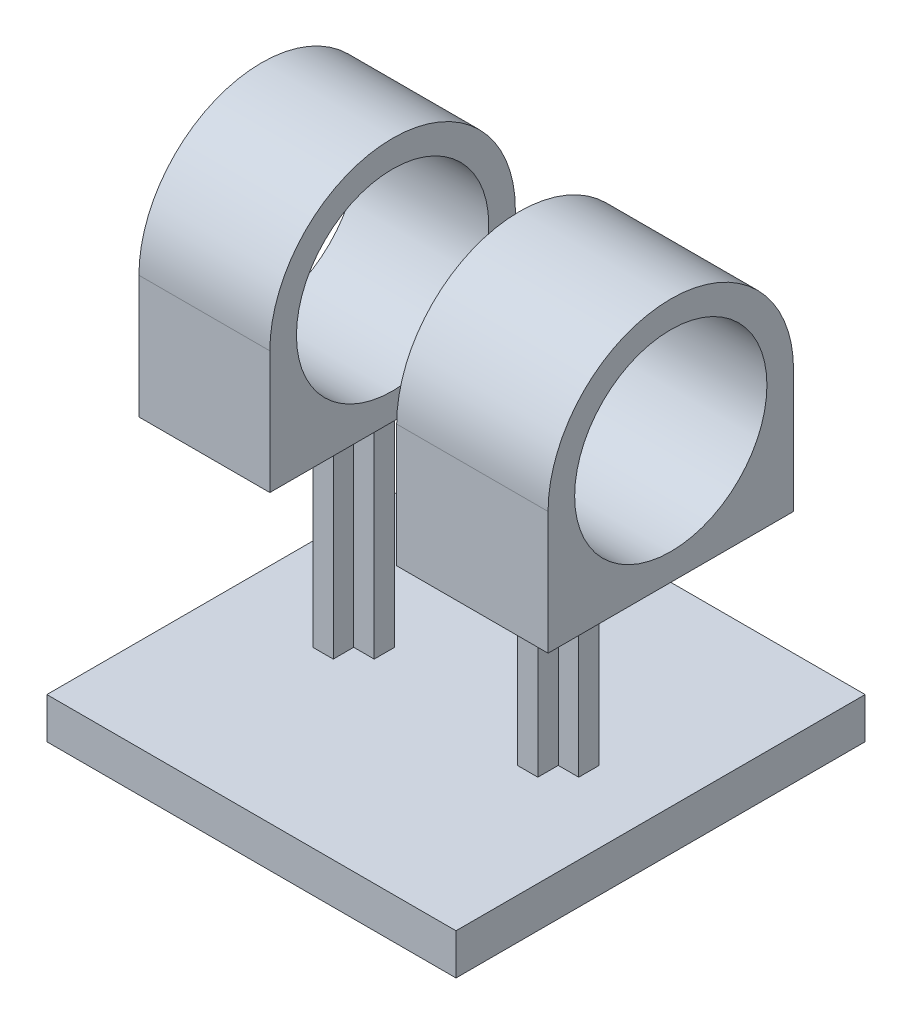
SolidWorks part; units mm, degrees
ref_plane "Plan de face" through (0, 0, 0) normal (0, 0, 1) x (1, 0, 0)
ref_plane "Plan de dessus" through (0, 0, 0) normal (0, 1, 0) x (1, 0, 0)
ref_plane "Plan de droite" through (0, 0, 0) normal (1, 0, 0) x (0, 0, -1)
sketch "Esquisse1" plane through (0, 0, 0) normal (0, 1, 0) x (1, 0, 0)
  line L1 (50, -50) -> (-50, -50)
  line L2 (50, -50) -> (50, 50)
  line L3 (50, 50) -> (-50, 50)
  line L4 (-50, -50) -> (-50, 50)
  line L5 (50, -50) -> (-50, 50) construction
  line L6 (50, 50) -> (-50, -50) construction
  point P0 (0, 0)
  dimension "D1" = 100
extrude "Boss.-Extru.1" add sketch "Esquisse1" along normal blind 10
sketch "Esquisse2" plane through (0, 10, 0) normal (0, 1, 0) x (1, 0, 0)
  line L0 (-25, 0) -> (25, 0) construction
  line L1 (-27.5, 2.5) -> (-27.5, 7.5)
  line L2 (-22.5, -7.5) -> (-27.5, -7.5)
  line L3 (-22.5, -7.5) -> (-22.5, -2.5)
  line L4 (-22.5, 7.5) -> (-27.5, 7.5)
  line L5 (-27.5, -7.5) -> (-27.5, -2.5)
  line L6 (-27.5, 2.5) -> (-22.5, -2.5) construction
  line L7 (-22.5, 2.5) -> (-22.5, 7.5)
  line L8 (-17.5, -2.5) -> (-22.5, -2.5)
  line L9 (-17.5, -2.5) -> (-17.5, 2.5)
  line L10 (-17.5, 2.5) -> (-22.5, 2.5)
  line L11 (-32.5, -2.5) -> (-32.5, 2.5)
  line L12 (-27.5, -2.5) -> (-22.5, 2.5) construction
  line L13 (0, -1000) -> (0, 49000) construction
  line L14 (27.5, -7.5) -> (27.5, -2.5)
  line L15 (-27.5, -2.5) -> (-32.5, -2.5)
  line L16 (-27.5, 2.5) -> (-32.5, 2.5)
  line L17 (22.5, -7.5) -> (27.5, -7.5)
  line L18 (22.5, -7.5) -> (22.5, -2.5)
  line L19 (17.5, -2.5) -> (22.5, -2.5)
  line L20 (17.5, -2.5) -> (17.5, 2.5)
  line L21 (17.5, 2.5) -> (22.5, 2.5)
  line L22 (22.5, 2.5) -> (22.5, 7.5)
  line L23 (22.5, 7.5) -> (27.5, 7.5)
  line L24 (27.5, 2.5) -> (27.5, 7.5)
  line L25 (27.5, 2.5) -> (32.5, 2.5)
  line L26 (32.5, -2.5) -> (32.5, 2.5)
  line L27 (27.5, -2.5) -> (32.5, -2.5)
  point P3 (-25, 0)
  point P4 (0, 0)
  dimension "D1" = 50
  dimension "D2" = 5
extrude "Boss.-Extru.2" add sketch "Esquisse2" along normal blind 50
sketch "Esquisse3" plane through (32.5, 0, 0) normal (1, 0, 0) x (0, 0, -1)
  line L0 (0, 60) -> (0, 90) construction
  line L1 (-2.5, 60) -> (2.5, 60) construction
  line L2 (0, 60) -> (-30, 60)
  line L3 (-30, 60) -> (-30, 90)
  line L4 (0, 60) -> (30, 60)
  line L5 (30, 60) -> (30, 90)
  arc A0 (30, 90) -> (-30, 90) centre (0, 90) ccw
  circle A1 centre (0, 90) radius 23.5
  point P7 (0, 120)
  dimension "D2" = 47
  dimension "D1" = 30
  dimension "D3" = 60
extrude "Boss.-Extru.3" add sketch "Esquisse3" along normal blind 20 and the other way blind 80 separate body
sketch "Esquisse4" plane through (0, 0, -30) normal (0, 0, -1) x (-1, 0, 0)
  line L0 (47.5, 60) -> (-52.5, 60) construction
  line L2 (15.5, 60) -> (15.5, 120)
  line L3 (15.5, 120) -> (-15.5, 120)
  line L4 (-15.5, 60) -> (-15.5, 120)
  line L7 (47.5, 120) -> (-52.5, 120) construction
  line L8 (-15.5, 60) -> (15.5, 60)
  line L9 (17.5, 60) -> (17.5, 10) construction
  line L10 (-17.5, 60) -> (-17.5, 10) construction
  point P14 (-4.72, 60)
  dimension "D1" = 2
  dimension "D2" = 2
extrude "Enlèv. mat.-Extru.1" cut sketch "Esquisse4" against normal blind 60
